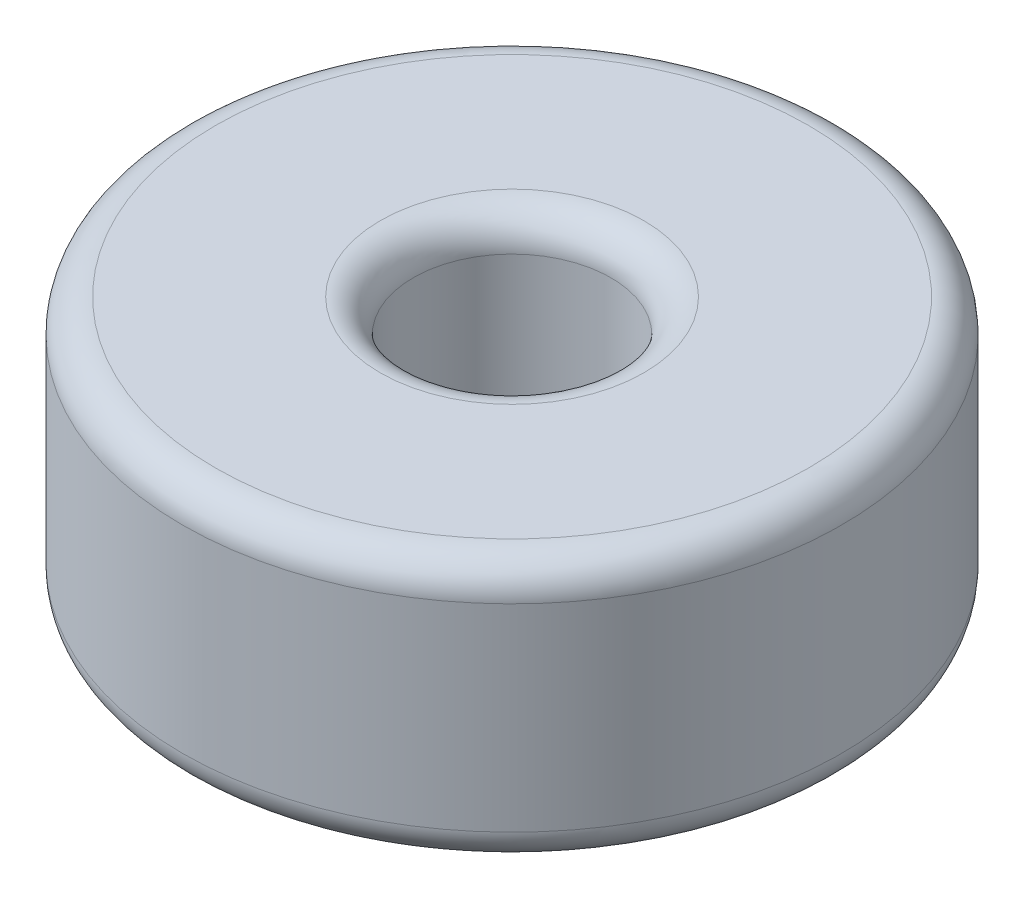
SolidWorks part; units mm, degrees
ref_plane "Front Plane" through (0, 0, 0) normal (0, 0, 1) x (1, 0, 0)
ref_plane "Top Plane" through (0, 0, 0) normal (0, 1, 0) x (1, 0, 0)
ref_plane "Right Plane" through (0, 0, 0) normal (1, 0, 0) x (0, 0, -1)
sketch "Sketch1" plane through (0, 0, 0) normal (0, 1, 0) x (1, 0, 0)
  circle A0 centre (0, 0) radius 1.5
  circle A1 centre (0, 0) radius 5
  dimension "D1" = 3
  dimension "D2" = 10
extrude "Boss-Extrude1" add sketch "Sketch1" along normal blind 4
fillet "Fillet1" radius 0.5 4 edges at (0, 0, 1.5) (0, 4, 1.5) (0, 0, 5) (0, 4, 5)
